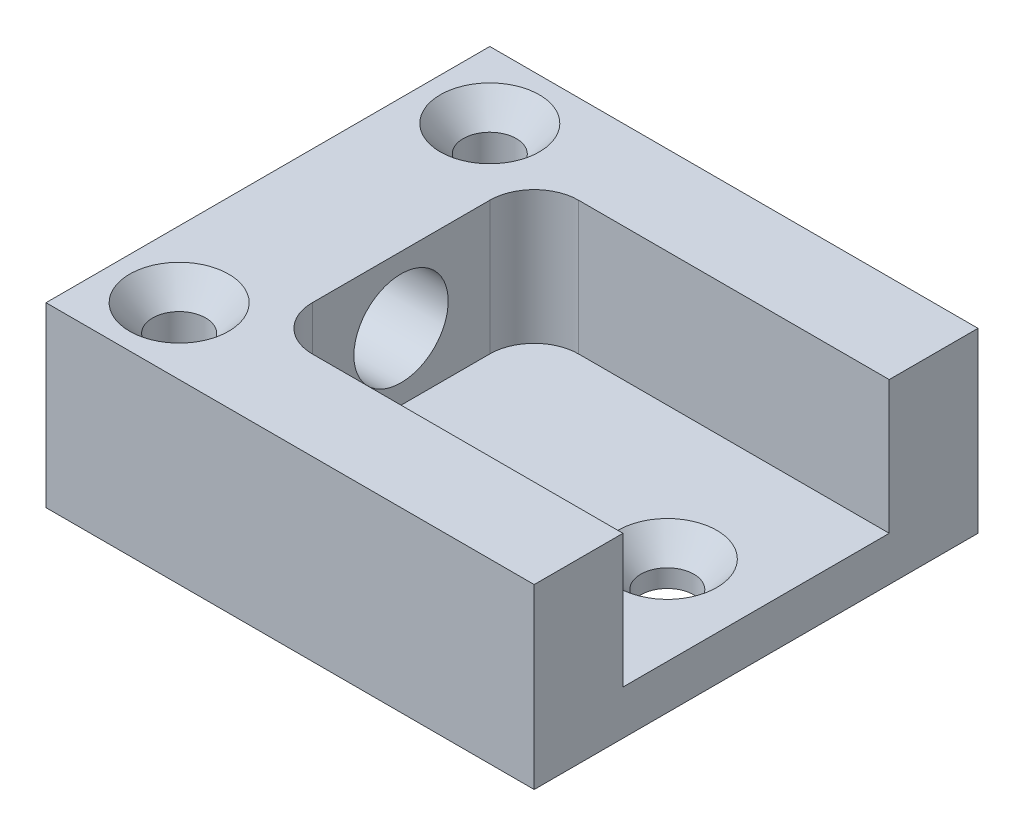
SolidWorks part; units mm, degrees
ref_plane "Front" through (0, 0, 0) normal (0, 0, 1) x (1, 0, 0)
ref_plane "Top" through (0, 0, 0) normal (0, 1, 0) x (1, 0, 0)
ref_plane "Right" through (0, 0, 0) normal (1, 0, 0) x (0, 0, -1)
sketch "Sketch1" plane through (0, 0, 0) normal (0, 1, 0) x (1, 0, 0)
  line L0 (0, 15.875) -> (0, -15.875)
  line L1 (0, -15.875) -> (34.925, -15.875)
  line L2 (34.925, -15.875) -> (34.925, -9.525)
  line L3 (34.925, -9.525) -> (9.525, -9.525)
  line L4 (9.525, -9.525) -> (9.525, 9.525)
  line L5 (9.525, 9.525) -> (34.925, 9.525)
  line L6 (34.925, 9.525) -> (34.925, 15.875)
  line L7 (34.925, 15.875) -> (0, 15.875)
  dimension "D1" = 19.05
  dimension "D2" = 6.35
  dimension "D3" = 25.4
  dimension "D4" = 9.525
extrude "Boss-Extrude1" add sketch "Sketch1" along normal blind 12.7 contours L0 L1 L2 L3 L4 L5 L6 L7
sketch "Sketch2" plane through (0, 0, 0) normal (0, -1, 0) x (1, 0, 0)
  line L1 (9.525, 9.525) -> (34.925, 9.525)
  line L2 (9.525, 9.525) -> (9.525, -9.525)
  line L3 (9.525, -9.525) -> (34.925, -9.525)
  line L4 (34.925, 9.525) -> (34.925, -9.525)
extrude "Boss-Extrude2" add sketch "Sketch2" against normal blind 3.175
fillet "Fillet1" radius 3.175 2 edges at (9.525, 7.9375, 9.525) (9.525, 7.9375, -9.525)
hole_wizard "17/64 (0.26563) Diameter Hole1" positions "Sketch3" profile "Sketch4" hole size "17/64" standard "ANSI Inch" end condition through all
sketch "Sketch3" plane through (0, 0, 0) normal (-1, 0, 0) x (0, 0, 1)
  line L8 (6.35, 12.7) -> (-6.35, 12.7)
  line L9 (6.35, 3.175) -> (6.35, 12.7)
  line L10 (-6.35, 3.175) -> (6.35, 3.175)
  line L11 (-6.35, 12.7) -> (-6.35, 3.175)
  line L12 (6.35, 12.7) -> (-6.35, 12.7)
  line L13 (6.35, 3.175) -> (6.35, 12.7)
  line L14 (-6.35, 3.175) -> (6.35, 3.175)
  line L15 (-6.35, 12.7) -> (-6.35, 3.175)
  line L16 (-6.35, 12.7) -> (6.35, 3.175)
  point P0 (0, 7.9375)
  point P23 (0, 7.9375)
  dimension "D1" = 0
sketch "Sketch4" plane through (0, 7.9375, 0) normal (0, 1, 0) x (0, 0, 1)
  line L0 (0, 0) -> (0, 34.925)
  line L1 (0, 34.925) -> (3.3735, 34.925)
  line L2 (3.3735, 34.925) -> (3.3735, 0)
  line L5 (3.3735, 0) -> (0, 0)
  line L11 (0, -6.35) -> (0, 107.95) construction
  dimension "Thru Hole Dia." = 6.747
  dimension "Thru Hole Depth" = 34.925
hole_wizard "CSK for #6 Flat Head Machine Screw1" positions "Sketch5" profile "Sketch6" countersink size "#6" standard "ANSI Inch"
sketch "Sketch5" plane through (0, 12.7, 0) normal (0, 1, 0) x (1, 0, 0)
  line L2 (4.7625, 11.1125) -> (4.7625, -11.1125)
  line L5 (0, 15.875) -> (0, -15.875) construction
  line L9 (0, -15.875) -> (34.925, -15.875) construction
  point P0 (4.7625, -11.1125)
  point P2 (4.7625, 11.1125)
  point P43 (0, 0)
  point P44 (0, 0)
  point P45 (0, 0)
  point P48 (4.7625, 0)
  point P49 (0, 0)
  dimension "D1" = 4.7625
  dimension "D2" = 4.7625
sketch "Sketch6" plane through (4.7625, 12.7, 11.1125) normal (1, 0, 0) x (0, 0, 1)
  line L0 (0, 0) -> (0, 17.6508)
  line L1 (0, 17.6508) -> (1.8986, 16.51)
  line L2 (1.8986, 16.51) -> (1.8986, 1.892)
  line L3 (1.8986, 1.892) -> (3.5433, 0)
  line L5 (3.5433, 0) -> (0, 0)
  line L6 (-1.8986, 1.892) -> (-3.5433, 0) construction
  line L10 (0, 17.6508) -> (-1.8987, 16.51) construction
  line L11 (0, -6.35) -> (0, 107.95) construction
  dimension "Hole Dia." = 3.7973
  dimension "Hole Depth" = 16.51
  dimension "Near C'Sink Dia." = 7.0866
  dimension "Near C'Sink Angle" = 82
  dimension "Drill Angle" = 118
hole_wizard "CSK for #6 Flat Head Machine Screw2" positions "Sketch7" profile "Sketch8" countersink size "#6" standard "ANSI Inch"
sketch "Sketch7" plane through (0, 3.175, 0) normal (0, 1, 0) x (1, 0, 0)
  line L0 (34.925, 9.525) -> (34.925, -9.525) construction
  point P0 (28.575, 0)
  point P5 (0, 0)
  dimension "D1" = 6.35
sketch "Sketch8" plane through (28.575, 3.175, 0) normal (1, 0, 0) x (0, 0, 1)
  line L0 (0, 0) -> (0, 17.6508)
  line L1 (0, 17.6508) -> (1.8986, 16.51)
  line L2 (1.8986, 16.51) -> (1.8986, 1.892)
  line L3 (1.8986, 1.892) -> (3.5433, 0)
  line L5 (3.5433, 0) -> (0, 0)
  line L6 (-1.8986, 1.892) -> (-3.5433, 0) construction
  line L10 (0, 17.6508) -> (-1.8986, 16.51) construction
  line L11 (0, -6.35) -> (0, 107.95) construction
  dimension "Hole Dia." = 3.7973
  dimension "Hole Depth" = 16.51
  dimension "Near C'Sink Dia." = 7.0866
  dimension "Near C'Sink Angle" = 82
  dimension "Drill Angle" = 118
